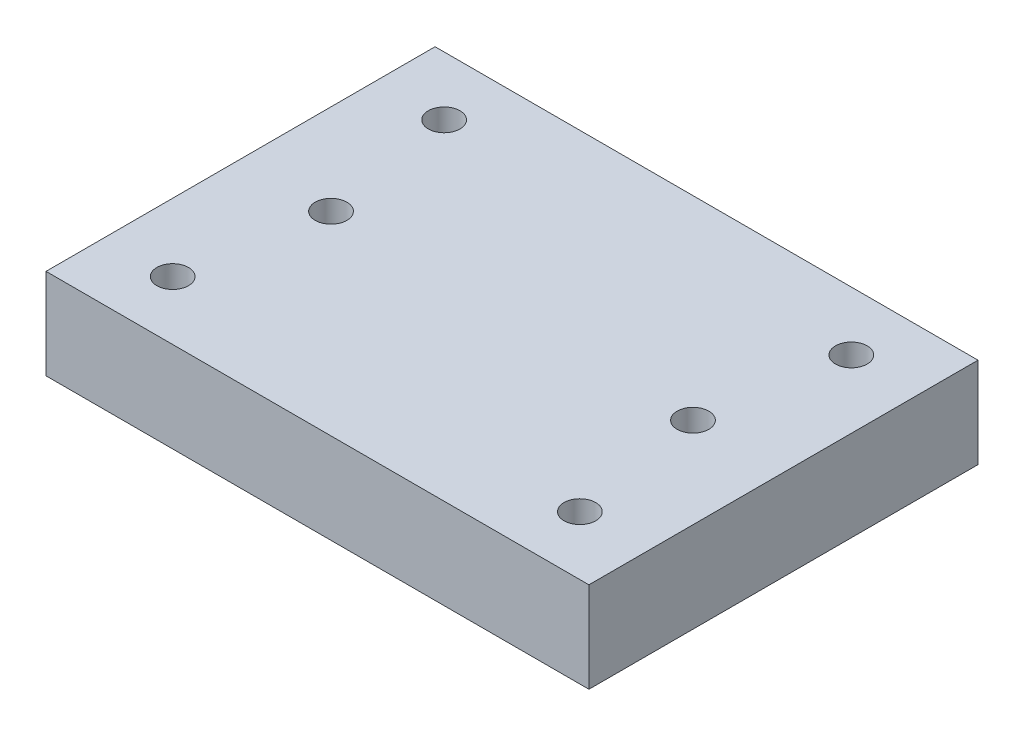
SolidWorks part; units mm, degrees
ref_plane "前视基准面" through (0, 0, 0) normal (0, 0, 1) x (1, 0, 0)
ref_plane "上视基准面" through (0, 0, 0) normal (0, 1, 0) x (1, 0, 0)
ref_plane "右视基准面" through (0, 0, 0) normal (1, 0, 0) x (0, 0, -1)
sketch "草图2" plane through (0, 0, 0) normal (0, 1, 0) x (1, 0, 0)
  line L1 (-30, -21.5) -> (30, -21.5)
  line L2 (-30, -21.5) -> (-30, 21.5)
  line L3 (-30, 21.5) -> (30, 21.5)
  line L4 (30, -21.5) -> (30, 21.5)
  line L5 (-30, -21.5) -> (30, 21.5) construction
  line L6 (-30, 21.5) -> (30, -21.5) construction
  point P0 (0, 0)
  dimension "D1" = 60
  dimension "D2" = 43
extrude "凸台-拉伸1" add sketch "草图2" along normal blind 10
sketch "草图3" plane through (0, 10, 0) normal (0, 1, 0) x (1, 0, 0)
  line L0 (0, -32.7287) -> (0, 32.7287) construction
  line L1 (-36.7336, 0) -> (36.7336, 0) construction
  circle A0 centre (-22.5, 15) radius 1.75
  circle A1 centre (22.5, 15) radius 1.75
  circle A2 centre (22.5, -15) radius 1.75
  circle A3 centre (-22.5, -15) radius 1.75
  point P4 (0, 0)
  point P8 (0, 0)
  dimension "D1" = 3.5
  dimension "D2" = 45
  dimension "D3" = 30
extrude "切除-拉伸1" cut sketch "草图3" against normal through all
sketch "草图4" plane through (0, 10, 0) normal (0, 1, 0) x (1, 0, 0)
  line L0 (0, 0) -> (0, -33.2496) construction
  circle A0 centre (-20, 0) radius 1.75
  circle A1 centre (20, 0) radius 1.75
  dimension "D1" = 3.5
  dimension "D2" = 3.5
  dimension "D3" = 40
extrude "切除-拉伸2" cut sketch "草图4" against normal through all
